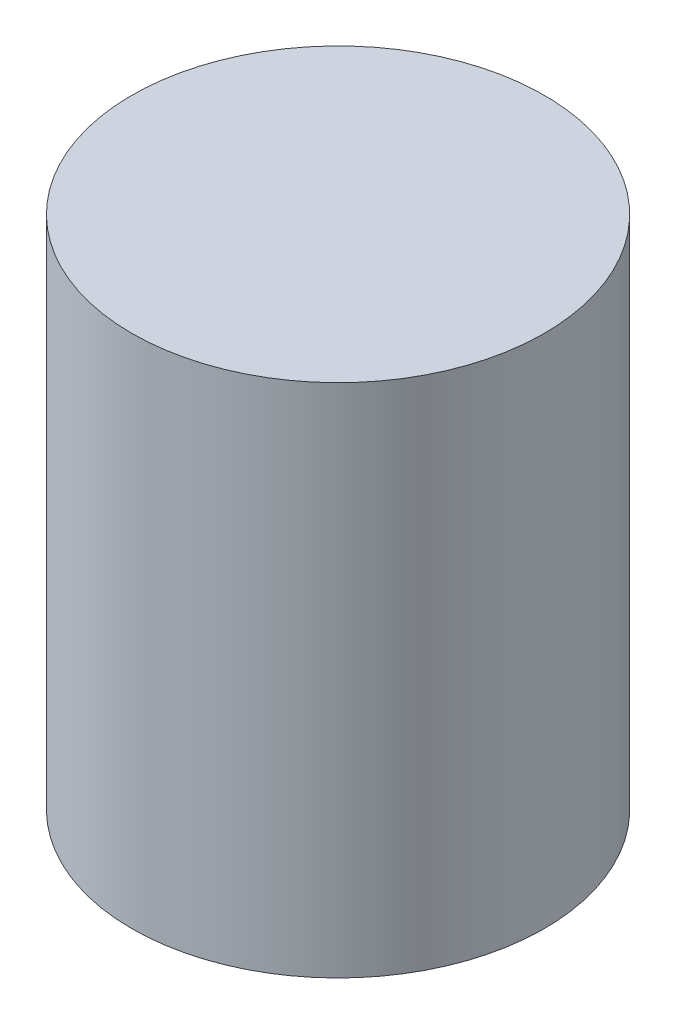
SolidWorks part; units mm, degrees
ref_plane "Front Plane" through (0, 0, 0) normal (0, 0, 1) x (1, 0, 0)
ref_plane "Top Plane" through (0, 0, 0) normal (0, 1, 0) x (1, 0, 0)
ref_plane "Right Plane" through (0, 0, 0) normal (1, 0, 0) x (0, 0, -1)
sketch "Sketch1" plane through (0, 0, 0) normal (0, 1, 0) x (1, 0, 0)
  circle A0 centre (0, 0) radius 3.81
  dimension "D1" = 7.62
extrude "Boss-Extrude1" add sketch "Sketch1" along normal blind 9.525
